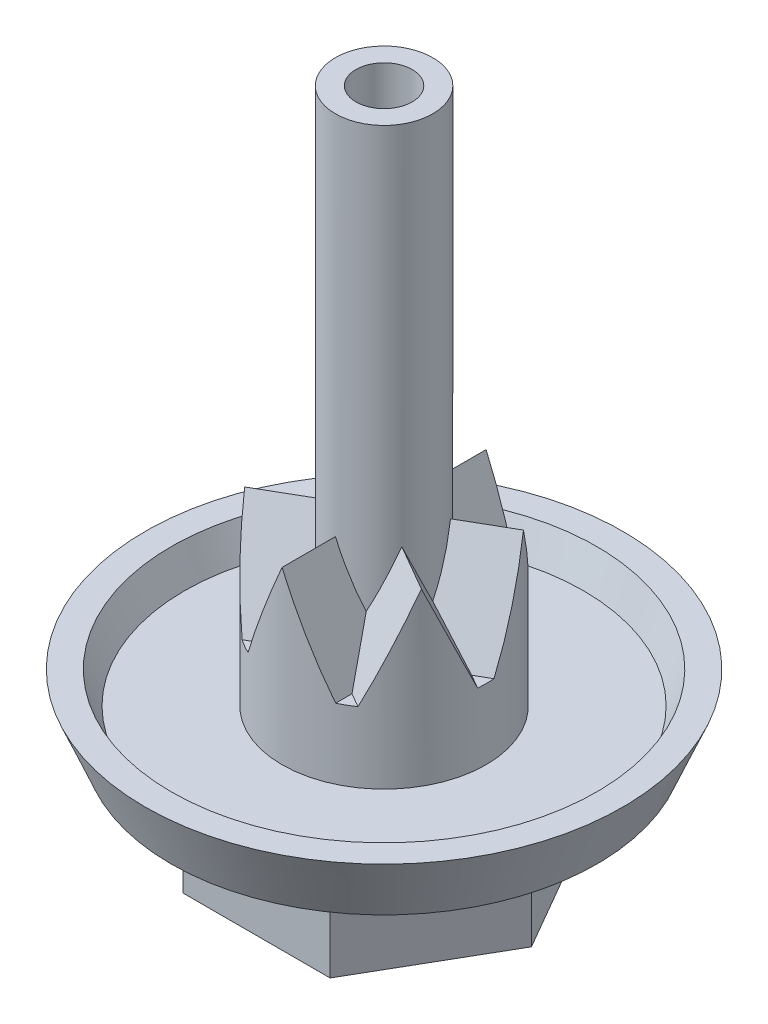
SolidWorks part; units mm, degrees
ref_plane "Front Plane" through (0, 0, 0) normal (0, 0, 1) x (1, 0, 0)
ref_plane "Top Plane" through (0, 0, 0) normal (0, 1, 0) x (1, 0, 0)
ref_plane "Right Plane" through (0, 0, 0) normal (1, 0, 0) x (0, 0, -1)
sketch "Sketch1" plane through (0, 0, 0) normal (0, 1, 0) x (1, 0, 0)
  line L0 (-55, 0) -> (55, 0) construction
  line L1 (-3.5738, 6.19) -> (-7.1476, 0)
  line L2 (-7.1476, 0) -> (-3.5738, -6.19)
  line L3 (-3.5738, -6.19) -> (3.5738, -6.19)
  line L4 (3.5738, -6.19) -> (7.1476, 0)
  line L5 (7.1476, 0) -> (3.5738, 6.19)
  line L6 (3.5738, 6.19) -> (-3.5738, 6.19)
  circle A0 centre (0, 0) radius 6.19 construction
  dimension "D1" = 12.38
extrude "Boss-Extrude1" add sketch "Sketch1" along normal blind 5.07
sketch "Sketch2" plane through (0, 5.07, 0) normal (0, 1, 0) x (1, 0, 0)
  circle A0 centre (0, 0) radius 11.585
  dimension "D1" = 23.17
extrude "Boss-Extrude2" add sketch "Sketch2" along normal blind 3.02
sketch "Sketch3" plane through (0, 0, 0) normal (0, 0, 1) x (1, 0, 0)
  line L1 (-11.585, 5.07) -> (11.585, 5.07) construction
  line L2 (10.33, 5.07) -> (11.585, 5.07)
  line L3 (11.585, 5.07) -> (11.585, 8.09)
  line L4 (10.33, 5.07) -> (11.585, 8.09)
  line L5 (0, 10.4928) -> (0, -4.7691) construction
  dimension "D1" = 10.33
revolve "Cut-Revolve1" cut sketch "Sketch3" angle 360 about L5
sketch "Sketch5" plane through (0, 0, 0) normal (0, 0, 1) x (1, 0, 0)
  line L0 (10.315, 8.09) -> (9.675, 6.55)
  line L1 (11.585, 8.09) -> (-11.585, 8.09) construction
  line L3 (10.33, 5.07) -> (11.585, 8.09) construction
  line L4 (9.675, 6.55) -> (4.95, 6.55)
  line L5 (0, -4.4495) -> (0, 4.4495) construction
  line L6 (4.95, 6.55) -> (4.95, 8.2735)
  line L7 (4.95, 8.2735) -> (10.315, 8.2735)
  line L8 (10.315, 8.2735) -> (10.315, 8.09)
  line L9 (0, 10.3465) -> (0, -0.6134) construction
  dimension "D1" = 1.27
  dimension "D2" = 1.54
  dimension "D3" = 4.95
revolve "Cut-Revolve2" cut sketch "Sketch5" angle 360 about L9
ref_plane "Plane1" through (4.95, 0, 0) normal (1, 0, 0) x (0, 0, -1)
sketch "Sketch10" plane through (5.3607, 0, -3.095) normal (0.866, 0, -0.5) x (-0.5, 0, -0.866)
  line L0 (-3.5738, 0) -> (0, 2.17)
  line L1 (-3.5738, 5.07) -> (-3.5738, 0) construction
  line L2 (0, 2.17) -> (3.5738, 0)
  line L3 (3.5738, 5.07) -> (3.5738, 0) construction
  line L4 (12.7435, 0) -> (-12.7435, 0) construction
  line L5 (-3.5738, 0) -> (3.5738, 0)
  dimension "D1" = 2.17
sketch "Sketch11" plane through (0, 0, 0) normal (0, -1, 0) x (1, 0, 0)
  line L0 (8.25, 0) -> (-8.25, 0) construction
  line L1 (-2.7568, 4.775) -> (-5.5137, 0)
  line L2 (-5.5137, 0) -> (-2.7568, -4.775)
  line L3 (-2.7568, -4.775) -> (2.7568, -4.775)
  line L4 (2.7568, -4.775) -> (5.5137, 0)
  line L5 (5.5137, 0) -> (2.7568, 4.775)
  line L6 (2.7568, 4.775) -> (-2.7568, 4.775)
  circle A0 centre (0, 0) radius 4.775 construction
  dimension "D1" = 9.55
extrude "Cut-Extrude3" cut sketch "Sketch11" against normal blind 5.28
sketch "Sketch12" plane through (0, 0, 0) normal (0, -1, 0) x (1, 0, 0)
  line L0 (-2.7568, 4.775) -> (-5.5137, 0) construction
  circle A0 centre (0, 0) radius 4.775
extrude "Cut-Extrude4" cut sketch "Sketch12" against normal blind 8.48
sketch "Sketch14" plane through (0, 8.09, 0) normal (0, 1, 0) x (1, 0, 0)
  circle A0 centre (0, 0) radius 2.36
  dimension "D1" = 4.72
extrude "Boss-Extrude5" add sketch "Sketch14" along normal blind 24.51 separate body
sketch "Sketch15" plane through (0, 8.09, 0) normal (0, 1, 0) x (1, 0, 0)
  circle A0 centre (0, 0) radius 4.95
  dimension "D1" = 9.9
extrude "Boss-Extrude6" add sketch "Sketch15" along normal blind 1.87
sketch "Sketch16" plane through (0, 0, 0) normal (0, 0, 1) x (1, 0, 0)
  line L0 (0, -4.2827) -> (0, 33.9627) construction
  line L1 (0, -12.7435) -> (0, 12.7435) construction
  line L2 (0, 14.84) -> (-2.125, 9.96)
  line L3 (4.95, 9.96) -> (-4.95, 9.96) construction
  line L4 (0, 14.84) -> (2.125, 9.96)
  line L5 (-2.125, 9.96) -> (2.125, 9.96)
  point P9 (0, 0)
  dimension "D1" = 2.125
  dimension "D2" = 2.125
  dimension "D3" = 4.88
extrude "Boss-Extrude7" add sketch "Sketch16" along normal up to surface (4.95 mm away) up to face at (0, 6.55, 4.95)
pattern_circular "CirPattern2" count 6 over 360 about axis through (0, 0, 0) along (0, 1, 0) of "Boss-Extrude7"
sketch "Sketch17" plane through (0, 32.6, 0) normal (0, 1, 0) x (1, 0, 0)
  circle A0 centre (0, 0) radius 1.3635
extrude "Cut-Extrude6" cut sketch "Sketch17" against normal offset from surface (22.64 mm away) 1.87 up to face at (0, 8.09, 4.775)
